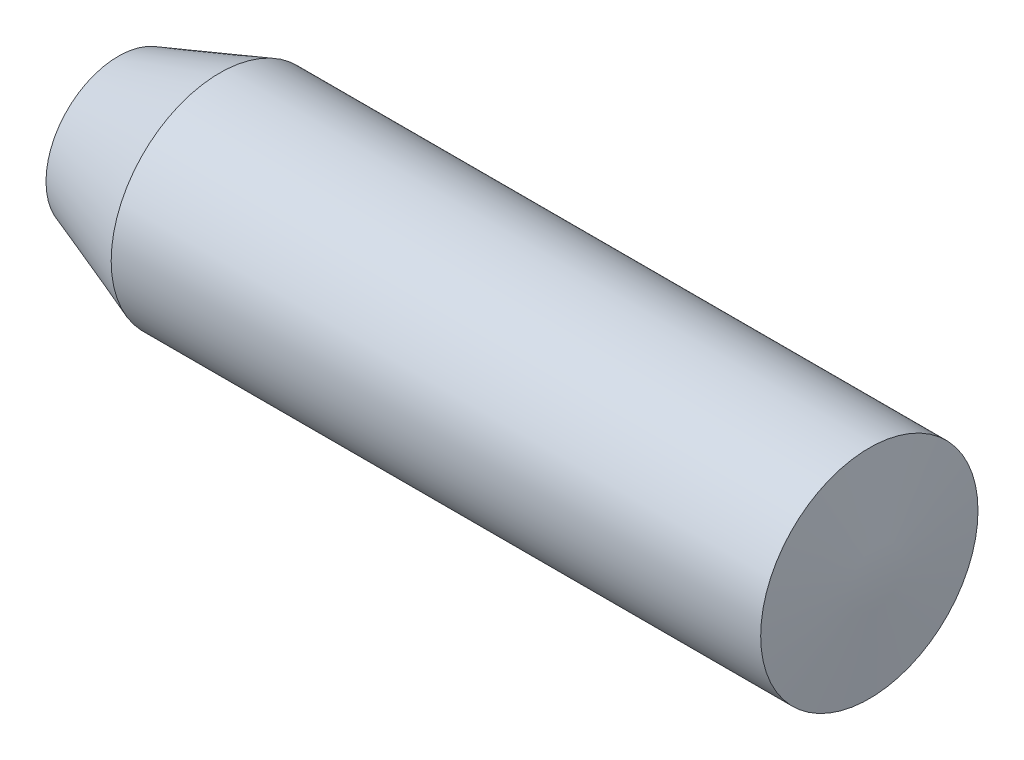
SolidWorks part; units mm, degrees
material "Cast Alloy Steel"
ref_plane "Front Plane" through (0, 0, 0) normal (0, 0, 1) x (1, 0, 0)
ref_plane "Top Plane" through (0, 0, 0) normal (0, 1, 0) x (1, 0, 0)
ref_plane "Right Plane" through (0, 0, 0) normal (1, 0, 0) x (0, 0, -1)
sketch "Sketch1" plane through (0, 0, 0) normal (0, 0, 1) x (1, 0, 0)
  line L0 (0, 0) -> (1778, 0) construction
  line L1 (0, 0) -> (0, 169.0969)
  line L2 (0, 169.0969) -> (237.2457, 254)
  line L3 (237.2457, 254) -> (1755.5085, 254)
  line L4 (1755.5085, 254) -> (1778, 0)
  line L5 (0, 0) -> (1778, 0)
  point P5 (889, 0)
  dimension "D1" = 1778
  dimension "D2" = 508
revolve "Revolve1" add sketch "Sketch1" angle 360 about L0
